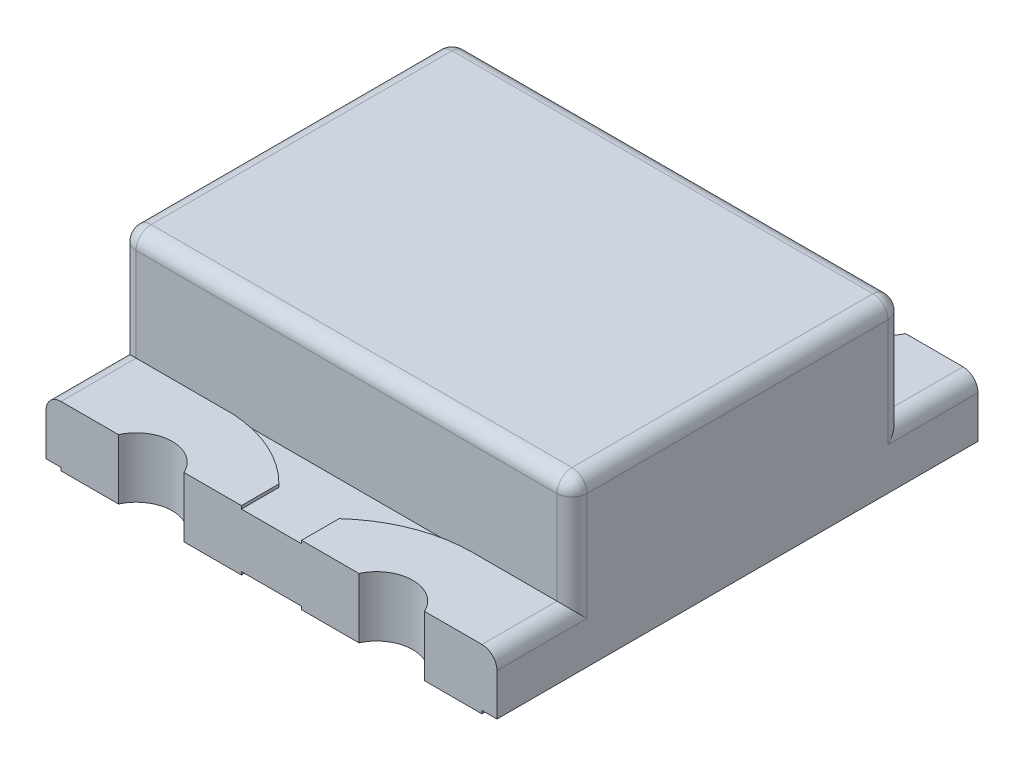
SolidWorks part; units mm, degrees
ref_plane "Front Plane" through (0, 0, 0) normal (0, 0, 1) x (1, 0, 0)
ref_plane "Top Plane" through (0, 0, 0) normal (0, 1, 0) x (1, 0, 0)
ref_plane "Right Plane" through (0, 0, 0) normal (1, 0, 0) x (0, 0, -1)
sketch "Sketch1" plane through (0, 0, 0) normal (0, 1, 0) x (1, 0, 0)
  line L1 (0, 0) -> (1.5, 0)
  line L2 (0, 0) -> (0, 1.6)
  line L3 (0, 1.6) -> (1.5, 1.6)
  line L4 (1.5, 0) -> (1.5, 1.6)
  dimension "D1" = 1.5
  dimension "D2" = 1.6
extrude "Boss-Extrude1" add sketch "Sketch1" along normal blind 0.18
sketch "Sketch2" plane through (0, 0, 0) normal (0, 1, 0) x (1, 0, 0)
  line L3 (1.5, 0) -> (1.5, 1.6) construction
  line L4 (0, 1.3505) -> (1.5, 1.3505)
  line L5 (0, 1.3505) -> (0, 0.2495)
  line L6 (0, 0.2495) -> (1.5, 0.2495)
  line L7 (1.5, 1.3505) -> (1.5, 0.2495)
  line L8 (0, 1.3505) -> (1.5, 0.2495) construction
  line L9 (0, 0.2495) -> (1.5, 1.3505) construction
  point P6 (0.75, 0.8)
extrude "Boss-Extrude2" add sketch "Sketch2" along normal blind 0.55
fillet "Fillet1" radius 0.05 2 edges at (0.75, 0.55, -1.3505) (0.75, 0.55, -0.2495)
sketch "Sketch3" plane through (0, 0, 0) normal (0, 1, 0) x (1, 0, 0)
  line L1 (1.5, 1.6) -> (0, 1.6) construction
  line L2 (0.85, 1.6) -> (0.85, 1.4752)
  line L3 (0.65, 1.4752) -> (0.65, 1.6)
  line L4 (0.65, 1.6) -> (0, 1.6)
  line L5 (0, 1.6) -> (0, 1.3505)
  line L6 (0.325, 1.3505) -> (0, 1.3505)
  line L7 (1.175, 1.3505) -> (1.5, 1.3505)
  line L8 (0.85, 1.6) -> (1.5, 1.6)
  line L11 (1.5, 1.6) -> (1.5, 1.3505)
  arc A0 (0.65, 1.4752) -> (0.325, 1.3505) centre (0.3496, 1.7721) cw
  arc A1 (0.85, 1.4752) -> (1.175, 1.3505) centre (1.1705, 1.8245) ccw
extrude "Boss-Extrude4" add sketch "Sketch3" along normal blind 0.19
ref_plane "Plane1" through (0, 0, -0.8) normal (0, 0, 1) x (1, 0, 0)
mirror "Mirror1" about plane through (0, 0, -0.8) normal (0, 0, 1) of "Boss-Extrude4"
fillet "Fillet2" radius 0.05 14 edges at (0, 0.345, -1.3505) (0, 0.5354, -1.3358) (0, 0.55, -0.8) (0, 0.5354, -0.2642) (1.5, 0.345, -1.3505) (1.5, 0.5354, -1.3358) (1.5, 0.55, -0.8) (1.5, 0.5354, -0.2642) (0, 0.19, -0.1248) (0, 0.19, -1.4752) (1.5, 0.19, -1.4752) (1.5, 0.19, -0.1248) (0, 0.345, -0.2495) (1.5, 0.345, -0.2495)
sketch "Sketch6" plane through (0, 0, 0) normal (0, 1, 0) x (1, 0, 0)
  line L0 (1.1461, 0) -> (0.85, 0)
  line L1 (0, 0) -> (1.5, 0) construction
  line L2 (0.35, 0) -> (0.65, 0)
  line L3 (0.65, 0) -> (0.65, 0.4)
  line L4 (0.65, 0.4) -> (0.35, 0.4)
  line L5 (0.35, 0.4) -> (0.05, 0.4)
  line L6 (0.05, 0.4) -> (0.05, 0)
  line L7 (0, 0) -> (1.5, 0) construction
  line L8 (0.05, 0) -> (0.35, 0)
  line L9 (0.85, 0) -> (0.85, 0.4)
  line L10 (0.85, 0.4) -> (1.4549, 0.4)
  line L11 (1.4549, 0.4) -> (1.45, 0)
  line L12 (1.45, 0) -> (1.1461, 0)
extrude "Boss-Extrude5" add sketch "Sketch6" against normal blind 0.01
mirror "Mirror3" about plane through (0, 0, -0.8) normal (0, 0, 1) of "Boss-Extrude5"
sketch "Sketch4" plane through (0, 0.18, 0) normal (0, 1, 0) x (1, 0, 0)
  circle A0 centre (0.35, 1.65) radius 0.12
  circle A1 centre (1.15, 1.65) radius 0.12
extrude "Cut-Extrude1" cut sketch "Sketch4" against normal through all both and the other way through all
mirror "Mirror2" about plane through (0, 0, -0.8) normal (0, 0, 1) of "Cut-Extrude1"
